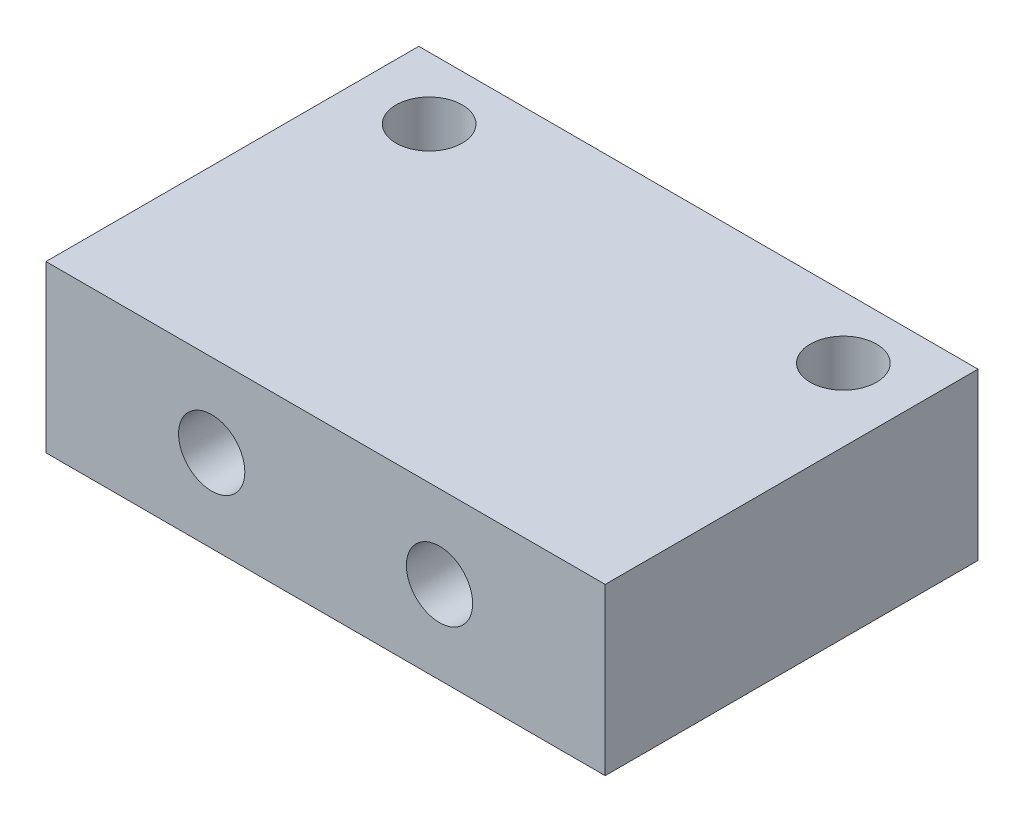
SolidWorks part; units mm, degrees
ref_plane "Front Plane" through (0, 0, 0) normal (0, 0, 1) x (1, 0, 0)
ref_plane "Top Plane" through (0, 0, 0) normal (0, 1, 0) x (1, 0, 0)
ref_plane "Right Plane" through (0, 0, 0) normal (1, 0, 0) x (0, 0, -1)
sketch "Sketch1" plane through (0, 0, 0) normal (0, 1, 0) x (1, 0, 0)
  line L0 (0, 0) -> (20, 0) construction
  line L2 (-3.5, -3) -> (23.5, -3)
  line L3 (-3.5, -3) -> (-3.5, 3)
  line L4 (-3.5, 3) -> (23.5, 3)
  line L5 (23.5, -3) -> (23.5, 3)
  line L6 (-3.5, -3) -> (23.5, 3) construction
  line L7 (-3.5, 3) -> (23.5, -3) construction
  circle A0 centre (0, 0) radius 1.6
  circle A1 centre (20, 0) radius 1.6
  point P5 (10, 0)
  dimension "D1" = 3.2
  dimension "D3" = 6
  dimension "D2" = 20
  dimension "D4" = 27
extrude "Boss-Extrude1" add sketch "Sketch1" along normal blind 8
sketch "Sketch3" plane through (0, 0, 3) normal (0, 0, 1) x (1, 0, 0)
  line L1 (-3.5, 0) -> (23.5, 0)
  line L2 (-3.5, 0) -> (-3.5, 8)
  line L3 (-3.5, 8) -> (23.5, 8)
  line L4 (23.5, 0) -> (23.5, 8)
extrude "Boss-Extrude2" add sketch "Sketch3" along normal blind 12
sketch "Sketch2" plane through (0, 0, 0) normal (0, 0, 1) x (1, 0, 0)
  line L0 (4.5, 8) -> (4.5, 0) construction
  line L3 (4.5, 4) -> (15.5, 4) construction
  line L4 (10, 0) -> (10, 8) construction
  line L5 (23.5, 8) -> (-3.5, 8) construction
  line L6 (-3.5, 0) -> (23.5, 0) construction
  circle A0 centre (4.5, 4) radius 1.6
  circle A1 centre (15.5, 4) radius 1.6
  point P13 (10, 4)
  dimension "D1" = 11
  dimension "D2" = 3.2
extrude "Cut-Extrude1" cut sketch "Sketch2" against normal through all both and the other way through all contours A0 | A1
